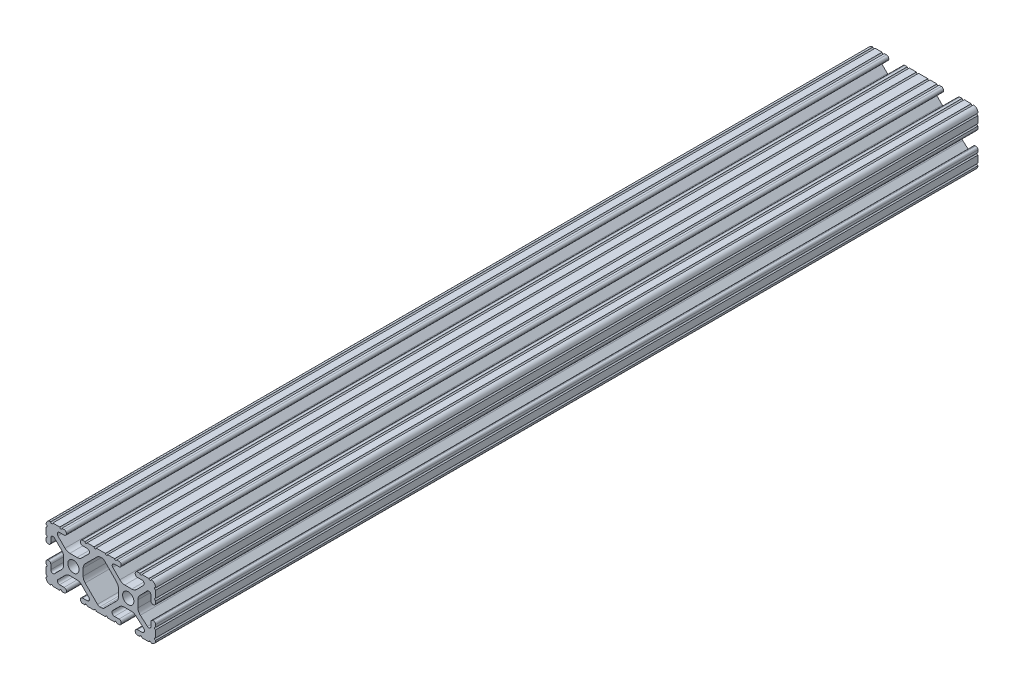
SolidWorks part; units mm, degrees
ref_plane "Front Plane" through (0, 0, 0) normal (0, 0, 1) x (1, 0, 0)
ref_plane "Top Plane" through (0, 0, 0) normal (0, 1, 0) x (1, 0, 0)
ref_plane "Right Plane" through (0, 0, 0) normal (1, 0, 0) x (0, 0, -1)
sketch "Sketch1" plane through (0, 0, 0) normal (0, 0, 1) x (1, 0, 0)
  line L0 (-7.2595, -3.8694) -> (-1.5457, -9.5728)
  line L1 (-8.1915, 1.6223) -> (-8.1915, -1.6223)
  line L2 (-1.504, 9.5765) -> (-7.252, 3.8768)
  line L3 (0.5515, 10.033) -> (-0.3952, 10.033)
  line L4 (7.2829, 3.8459) -> (1.6756, 9.5611)
  line L5 (8.1915, -1.6223) -> (8.1915, 1.6223)
  line L6 (1.5457, -9.5728) -> (7.2595, -3.8694)
  line L7 (-0.4332, -10.033) -> (0.4332, -10.033)
  line L8 (18.0171, 12.7) -> (16.9875, 12.7)
  line L9 (15.9385, 11.651) -> (15.9385, 11.5392)
  line L10 (16.9875, 10.4902) -> (19.1164, 10.4902)
  line L11 (19.8441, 8.7652) -> (16.619, 5.4551)
  line L12 (14.3449, 4.4958) -> (11.0833, 4.4958)
  line L13 (8.817, 5.4472) -> (5.5642, 8.7627)
  line L14 (6.2894, 10.4902) -> (8.4125, 10.4902)
  line L15 (9.4615, 11.5392) -> (9.4615, 11.651)
  line L16 (8.4125, 12.7) -> (7.3829, 12.7)
  line L17 (6.3669, 12.7) -> (3.1496, 12.7)
  line L18 (2.1336, 12.7) -> (-2.1336, 12.7)
  line L19 (-3.1496, 12.7) -> (-6.3669, 12.7)
  line L20 (-7.3829, 12.7) -> (-8.4125, 12.7)
  line L21 (-9.4615, 11.651) -> (-9.4615, 11.5392)
  line L22 (-8.4125, 10.4902) -> (-6.2836, 10.4902)
  line L23 (-5.5326, 8.6661) -> (-8.81, 5.4163)
  line L24 (-11.0455, 4.4958) -> (-14.3545, 4.4958)
  line L25 (-16.59, 5.4163) -> (-19.8674, 8.6661)
  line L26 (-19.1164, 10.4902) -> (-16.9875, 10.4902)
  line L27 (-15.9385, 11.5392) -> (-15.9385, 11.651)
  line L28 (-16.9875, 12.7) -> (-18.0171, 12.7)
  line L29 (-19.0331, 12.7) -> (-22.2504, 12.7)
  line L30 (-25.4, 9.5504) -> (-25.4, 6.3331)
  line L31 (-25.4, 5.3171) -> (-25.4, 4.2375)
  line L32 (-24.401, 3.2385) -> (-24.2392, 3.2385)
  line L33 (-23.1902, 4.2875) -> (-23.1902, 6.3347)
  line L34 (-21.434, 7.0665) -> (-18.148, 3.8082)
  line L35 (-17.2085, 1.5536) -> (-17.2085, -1.6952)
  line L36 (-18.1405, -3.9423) -> (-21.4316, -7.2274)
  line L37 (-23.1902, -6.498) -> (-23.1902, -4.2875)
  line L38 (-24.2392, -3.2385) -> (-24.351, -3.2385)
  line L39 (-25.4, -4.2875) -> (-25.4, -5.3171)
  line L40 (-25.4, -6.3331) -> (-25.4, -9.5504)
  line L41 (-22.2504, -12.7) -> (-19.0331, -12.7)
  line L42 (-18.0171, -12.7) -> (-16.9875, -12.7)
  line L43 (-15.9384, -11.651) -> (-15.9384, -11.5392)
  line L44 (-16.9875, -10.4902) -> (-19.1164, -10.4902)
  line L45 (-19.8341, -8.7551) -> (-16.4966, -5.4237)
  line L46 (-14.2536, -4.4958) -> (-11.1464, -4.4958)
  line L47 (-8.9034, -5.4237) -> (-5.5659, -8.7551)
  line L48 (-6.2836, -10.4902) -> (-8.4125, -10.4902)
  line L49 (-9.4616, -11.5392) -> (-9.4616, -11.651)
  line L50 (-8.4125, -12.7) -> (-7.3829, -12.7)
  line L51 (-6.3669, -12.7) -> (-3.1496, -12.7)
  line L52 (-2.1336, -12.7) -> (2.1336, -12.7)
  line L53 (3.1496, -12.7) -> (6.3669, -12.7)
  line L54 (7.3829, -12.7) -> (8.4125, -12.7)
  line L55 (9.4616, -11.651) -> (9.4616, -11.5392)
  line L56 (8.4125, -10.4902) -> (6.2894, -10.4902)
  line L57 (5.4807, -8.5353) -> (8.5979, -5.4237)
  line L58 (10.8409, -4.4958) -> (14.1026, -4.4958)
  line L59 (16.1879, -5.2766) -> (19.8682, -8.4822)
  line L60 (19.1164, -10.4902) -> (16.9875, -10.4902)
  line L61 (15.9384, -11.5392) -> (15.9384, -11.651)
  line L62 (16.9875, -12.7) -> (18.0171, -12.7)
  line L63 (19.0331, -12.7) -> (22.2504, -12.7)
  line L64 (25.4, -9.5504) -> (25.4, -6.3331)
  line L65 (25.4, -5.3171) -> (25.4, -4.2375)
  line L66 (24.401, -3.2385) -> (24.1892, -3.2385)
  line L67 (23.1902, -4.2375) -> (23.1902, -6.1559)
  line L68 (21.584, -6.8869) -> (18.2982, -4.025)
  line L69 (17.2085, -1.6308) -> (17.2085, 1.6308)
  line L70 (18.1094, 3.8465) -> (21.5263, 7.3534)
  line L71 (23.1902, 6.6769) -> (23.1902, 4.2375)
  line L72 (24.1892, 3.2385) -> (24.401, 3.2385)
  line L73 (25.4, 4.2375) -> (25.4, 5.3171)
  line L74 (25.4, 6.3332) -> (25.4, 9.5504)
  line L75 (22.2504, 12.7) -> (19.0331, 12.7)
  circle A0 centre (-12.7, 0) radius 2.6035
  circle A1 centre (12.7, 0) radius 2.6035
  arc A2 (-1.5457, -9.5728) -> (-0.4332, -10.033) centre (-0.4332, -8.4582) ccw
  arc A3 (-8.1915, -1.6223) -> (-7.2595, -3.8694) centre (-5.0165, -1.6223) ccw
  arc A4 (-7.252, 3.8768) -> (-8.1915, 1.6223) centre (-5.0165, 1.6223) ccw
  arc A5 (-0.3952, 10.033) -> (-1.504, 9.5765) centre (-0.3952, 8.4582) ccw
  arc A6 (1.6756, 9.5611) -> (0.5515, 10.033) centre (0.5515, 8.4582) ccw
  arc A7 (8.1915, 1.6223) -> (7.2829, 3.8459) centre (5.0165, 1.6223) ccw
  arc A8 (7.2595, -3.8694) -> (8.1915, -1.6223) centre (5.0165, -1.6223) ccw
  arc A9 (0.4332, -10.033) -> (1.5457, -9.5728) centre (0.4332, -8.4582) ccw
  arc A10 (18.0171, 12.7) -> (19.0331, 12.7) centre (18.5251, 12.7) ccw
  arc A11 (16.9875, 12.7) -> (15.9385, 11.651) centre (16.9875, 11.651) ccw
  arc A12 (15.9385, 11.5392) -> (16.9875, 10.4902) centre (16.9875, 11.5392) ccw
  arc A13 (19.8441, 8.7652) -> (19.1164, 10.4902) centre (19.1164, 9.4742) ccw
  arc A14 (14.3449, 4.4958) -> (16.619, 5.4551) centre (14.3449, 7.6708) ccw
  arc A15 (8.817, 5.4472) -> (11.0833, 4.4958) centre (11.0833, 7.6708) ccw
  arc A16 (6.2894, 10.4902) -> (5.5642, 8.7627) centre (6.2894, 9.4742) ccw
  arc A17 (8.4125, 10.4902) -> (9.4615, 11.5392) centre (8.4125, 11.5392) ccw
  arc A18 (9.4615, 11.651) -> (8.4125, 12.7) centre (8.4125, 11.651) ccw
  arc A19 (6.3669, 12.7) -> (7.3829, 12.7) centre (6.8749, 12.7) ccw
  arc A20 (2.1336, 12.7) -> (3.1496, 12.7) centre (2.6416, 12.7) ccw
  arc A21 (-3.1496, 12.7) -> (-2.1336, 12.7) centre (-2.6416, 12.7) ccw
  arc A22 (-7.3829, 12.7) -> (-6.3669, 12.7) centre (-6.8749, 12.7) ccw
  arc A23 (-8.4125, 12.7) -> (-9.4615, 11.651) centre (-8.4125, 11.651) ccw
  arc A24 (-9.4615, 11.5392) -> (-8.4125, 10.4902) centre (-8.4125, 11.5392) ccw
  arc A25 (-5.5326, 8.6661) -> (-6.2836, 10.4902) centre (-6.2836, 9.4235) ccw
  arc A26 (-11.0455, 4.4958) -> (-8.81, 5.4163) centre (-11.0455, 7.6708) ccw
  arc A27 (-16.59, 5.4163) -> (-14.3545, 4.4958) centre (-14.3545, 7.6708) ccw
  arc A28 (-19.1164, 10.4902) -> (-19.8674, 8.6661) centre (-19.1164, 9.4235) ccw
  arc A29 (-16.9875, 10.4902) -> (-15.9385, 11.5392) centre (-16.9875, 11.5392) ccw
  arc A30 (-15.9385, 11.651) -> (-16.9875, 12.7) centre (-16.9875, 11.651) ccw
  arc A31 (-19.0331, 12.7) -> (-18.0171, 12.7) centre (-18.5251, 12.7) ccw
  arc A32 (-23.2664, 12.6998) -> (-22.2504, 12.7) centre (-22.7584, 12.7) ccw
  arc A33 (-23.2664, 12.6998) -> (-25.3998, 10.5664) centre (-23.2918, 10.5918) ccw
  arc A34 (-25.4, 9.5504) -> (-25.3998, 10.5664) centre (-25.4, 10.0584) ccw
  arc A35 (-25.4, 5.3171) -> (-25.4, 6.3331) centre (-25.4, 5.8251) ccw
  arc A36 (-25.4, 4.2375) -> (-24.401, 3.2385) centre (-24.401, 4.2375) ccw
  arc A37 (-24.2392, 3.2385) -> (-23.1902, 4.2875) centre (-24.2392, 4.2875) ccw
  arc A38 (-21.434, 7.0665) -> (-23.1902, 6.3347) centre (-22.1596, 6.3347) ccw
  arc A39 (-17.2085, 1.5536) -> (-18.148, 3.8082) centre (-20.3835, 1.5536) ccw
  arc A40 (-18.1405, -3.9423) -> (-17.2085, -1.6952) centre (-20.3835, -1.6952) ccw
  arc A41 (-23.1902, -6.498) -> (-21.4316, -7.2274) centre (-22.1596, -6.498) ccw
  arc A42 (-23.1902, -4.2875) -> (-24.2392, -3.2385) centre (-24.2392, -4.2875) ccw
  arc A43 (-24.351, -3.2385) -> (-25.4, -4.2875) centre (-24.351, -4.2875) ccw
  arc A44 (-25.4, -6.3331) -> (-25.4, -5.3171) centre (-25.4, -5.8251) ccw
  arc A45 (-25.3998, -10.5664) -> (-25.4, -9.5504) centre (-25.4, -10.0584) ccw
  arc A46 (-25.3998, -10.5664) -> (-23.2664, -12.6998) centre (-23.2918, -10.5918) ccw
  arc A47 (-22.2504, -12.7) -> (-23.2664, -12.6998) centre (-22.7584, -12.7) ccw
  arc A48 (-18.0171, -12.7) -> (-19.0331, -12.7) centre (-18.5251, -12.7) ccw
  arc A49 (-16.9875, -12.7) -> (-15.9384, -11.651) centre (-16.9875, -11.651) ccw
  arc A50 (-15.9384, -11.5392) -> (-16.9875, -10.4902) centre (-16.9875, -11.5392) ccw
  arc A51 (-19.8341, -8.7551) -> (-19.1164, -10.4902) centre (-19.1164, -9.4742) ccw
  arc A52 (-14.2536, -4.4958) -> (-16.4966, -5.4237) centre (-14.2536, -7.6708) ccw
  arc A53 (-8.9034, -5.4237) -> (-11.1464, -4.4958) centre (-11.1464, -7.6708) ccw
  arc A54 (-6.2836, -10.4902) -> (-5.5659, -8.7551) centre (-6.2836, -9.4742) ccw
  arc A55 (-8.4125, -10.4902) -> (-9.4616, -11.5392) centre (-8.4125, -11.5392) ccw
  arc A56 (-9.4616, -11.651) -> (-8.4125, -12.7) centre (-8.4125, -11.651) ccw
  arc A57 (-6.3669, -12.7) -> (-7.3829, -12.7) centre (-6.8749, -12.7) ccw
  arc A58 (-2.1336, -12.7) -> (-3.1496, -12.7) centre (-2.6416, -12.7) ccw
  arc A59 (3.1496, -12.7) -> (2.1336, -12.7) centre (2.6416, -12.7) ccw
  arc A60 (7.3829, -12.7) -> (6.3669, -12.7) centre (6.8749, -12.7) ccw
  arc A61 (8.4125, -12.7) -> (9.4616, -11.651) centre (8.4125, -11.651) ccw
  arc A62 (9.4616, -11.5392) -> (8.4125, -10.4902) centre (8.4125, -11.5392) ccw
  arc A63 (5.4807, -8.5353) -> (6.2894, -10.4902) centre (6.2894, -9.3455) ccw
  arc A64 (10.8409, -4.4958) -> (8.5979, -5.4237) centre (10.8409, -7.6708) ccw
  arc A65 (16.1879, -5.2766) -> (14.1026, -4.4958) centre (14.1026, -7.6708) ccw
  arc A66 (19.1164, -10.4902) -> (19.8682, -8.4822) centre (19.1164, -9.3455) ccw
  arc A67 (16.9875, -10.4902) -> (15.9384, -11.5392) centre (16.9875, -11.5392) ccw
  arc A68 (15.9384, -11.651) -> (16.9875, -12.7) centre (16.9875, -11.651) ccw
  arc A69 (19.0331, -12.7) -> (18.0171, -12.7) centre (18.5251, -12.7) ccw
  arc A70 (23.2664, -12.6998) -> (22.2504, -12.7) centre (22.7584, -12.7) ccw
  arc A71 (23.2664, -12.6998) -> (25.3998, -10.5664) centre (23.2918, -10.5918) ccw
  arc A72 (25.4, -9.5504) -> (25.3998, -10.5664) centre (25.4, -10.0584) ccw
  arc A73 (25.4, -5.3171) -> (25.4, -6.3331) centre (25.4, -5.8251) ccw
  arc A74 (25.4, -4.2375) -> (24.401, -3.2385) centre (24.401, -4.2375) ccw
  arc A75 (24.1892, -3.2385) -> (23.1902, -4.2375) centre (24.1892, -4.2375) ccw
  arc A76 (21.584, -6.8869) -> (23.1902, -6.1559) centre (22.2207, -6.1559) ccw
  arc A77 (17.2085, -1.6308) -> (18.2982, -4.025) centre (20.3835, -1.6308) ccw
  arc A78 (18.1094, 3.8465) -> (17.2085, 1.6308) centre (20.3835, 1.6308) ccw
  arc A79 (23.1902, 6.6769) -> (21.5263, 7.3534) centre (22.2207, 6.6769) ccw
  arc A80 (23.1902, 4.2375) -> (24.1892, 3.2385) centre (24.1892, 4.2375) ccw
  arc A81 (24.401, 3.2385) -> (25.4, 4.2375) centre (24.401, 4.2375) ccw
  arc A82 (25.4, 6.3332) -> (25.4, 5.3171) centre (25.4, 5.8251) ccw
  arc A83 (25.3998, 10.5664) -> (25.4, 9.5504) centre (25.4, 10.0584) ccw
  arc A84 (25.3998, 10.5664) -> (23.2664, 12.6998) centre (23.2918, 10.5918) ccw
  arc A85 (22.2504, 12.7) -> (23.2664, 12.6998) centre (22.7584, 12.7) ccw
  point P248 (0, 10.033)
extrude "Boss-Extrude1" add sketch "Sketch1" along normal mid plane 381
